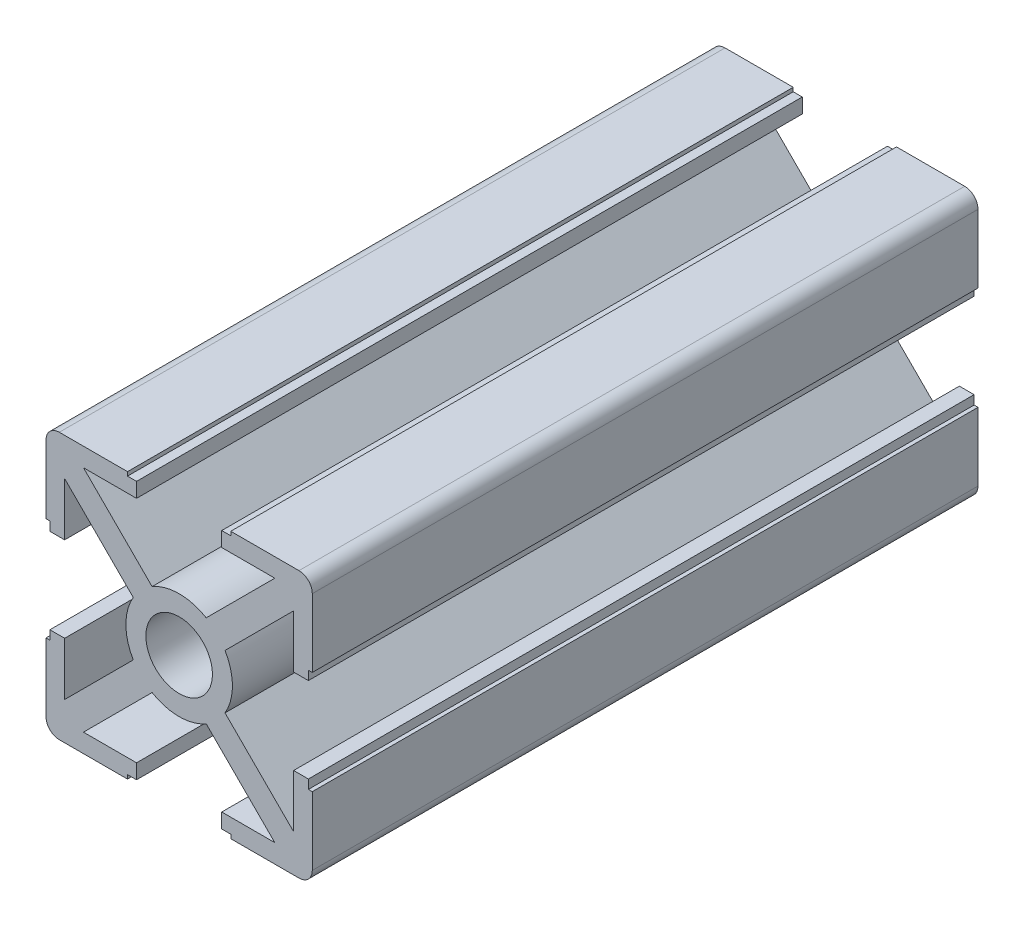
SolidWorks part; units mm, degrees
material "1060 Alloy"
ref_plane "Ön Düzlem" through (0, 0, 0) normal (0, 0, 1) x (1, 0, 0)
ref_plane "Üst Düzlem" through (0, 0, 0) normal (0, 1, 0) x (1, 0, 0)
ref_plane "Sağ Düzlem" through (0, 0, 0) normal (1, 0, 0) x (0, 0, -1)
sketch "Sketch1" plane through (0, 0, 0) normal (0, 0, 1) x (1, 0, 0)
  line L0 (-9.7071, -3.2) -> (-8.6, -3.2)
  line L2 (-10, -3.8775) -> (-10, -9)
  line L3 (-9, -10) -> (-3.8775, -10)
  line L5 (-10, -3.8775) -> (-9.7071, -3.8775)
  line L6 (-10, -10) -> (-9.7071, -9.7071) construction
  line L9 (-3.2, -8.6) -> (-7.1858, -8.6)
  line L10 (-8.6, -3.2) -> (-8.6, -7.1858)
  line L13 (-7.1858, -8.6) -> (-2.0315, -3.4457)
  line L14 (-8.6, -7.1858) -> (-3.4457, -2.0315)
  line L15 (-10.7071, -9.2929) -> (9.2929, 10.7071) construction
  line L16 (-9.2929, -10.7071) -> (10.7071, 9.2929) construction
  line L18 (-10, -10) -> (10, 10) construction
  line L19 (-2.5, 0) -> (-9.7071, 0) construction
  line L20 (0, -2.5) -> (0, -6.9362) construction
  line L21 (-3.2, -8.6) -> (-3.2, -9.7071)
  line L23 (-9.7071, -3.8775) -> (-9.7071, -3.2)
  line L24 (-3.2, -9.7071) -> (-3.8775, -9.7071)
  line L25 (-3.8775, -9.7071) -> (-3.8775, -10)
  line L28 (10, -10) -> (9.7071, -9.7071) construction
  line L30 (3.8775, -9.7071) -> (3.8775, -10)
  line L31 (3.2, -9.7071) -> (3.8775, -9.7071)
  line L32 (9.7071, -3.8775) -> (9.7071, -3.2)
  line L33 (3.2, -8.6) -> (3.2, -9.7071)
  line L34 (8.6, -7.1858) -> (3.4457, -2.0315)
  line L35 (7.1858, -8.6) -> (2.0315, -3.4457)
  line L36 (8.6, -3.2) -> (8.6, -7.1858)
  line L37 (3.2, -8.6) -> (7.1858, -8.6)
  line L38 (10, -3.8775) -> (9.7071, -3.8775)
  line L39 (9, -10) -> (3.8775, -10)
  line L40 (10, -3.8775) -> (10, -9)
  line L41 (9.7071, -3.2) -> (8.6, -3.2)
  line L42 (10, 10) -> (9.7071, 9.7071) construction
  line L43 (0, 2.5) -> (0, 6.9362) construction
  line L44 (-10, 10) -> (-9.7071, 9.7071) construction
  line L45 (9.7071, 3.2) -> (8.6, 3.2)
  line L46 (10, 3.8775) -> (10, 9)
  line L47 (9, 10) -> (3.8775, 10)
  line L48 (10, 3.8775) -> (9.7071, 3.8775)
  line L49 (3.2, 8.6) -> (7.1858, 8.6)
  line L50 (8.6, 3.2) -> (8.6, 7.1858)
  line L51 (7.1858, 8.6) -> (2.0315, 3.4457)
  line L52 (8.6, 7.1858) -> (3.4457, 2.0315)
  line L53 (3.2, 8.6) -> (3.2, 9.7071)
  line L54 (9.7071, 3.8775) -> (9.7071, 3.2)
  line L55 (3.2, 9.7071) -> (3.8775, 9.7071)
  line L56 (3.8775, 9.7071) -> (3.8775, 10)
  line L57 (-3.8775, 9.7071) -> (-3.8775, 10)
  line L58 (-3.2, 9.7071) -> (-3.8775, 9.7071)
  line L59 (-9.7071, 3.8775) -> (-9.7071, 3.2)
  line L60 (-3.2, 8.6) -> (-3.2, 9.7071)
  line L61 (-8.6, 7.1858) -> (-3.4457, 2.0315)
  line L62 (-7.1858, 8.6) -> (-2.0315, 3.4457)
  line L63 (-8.6, 3.2) -> (-8.6, 7.1858)
  line L64 (-3.2, 8.6) -> (-7.1858, 8.6)
  line L65 (-10, 3.8775) -> (-9.7071, 3.8775)
  line L66 (-9, 10) -> (-3.8775, 10)
  line L67 (-10, 3.8775) -> (-10, 9)
  line L68 (-9.7071, 3.2) -> (-8.6, 3.2)
  arc A2 (-10, -9) -> (-9, -10) centre (-9, -9) ccw
  arc A3 (-2.0315, -3.4457) -> (2.0315, -3.4457) centre (0, 0) ccw
  arc A4 (-3.4457, 2.0315) -> (-3.4457, -2.0315) centre (0, 0) ccw
  circle A5 centre (0, 0) radius 2.5
  arc A6 (3.4457, 2.0315) -> (3.4457, -2.0315) centre (0, 0) cw
  arc A7 (10, -9) -> (9, -10) centre (9, -9) cw
  arc A8 (10, 9) -> (9, 10) centre (9, 9) ccw
  arc A9 (-2.0315, 3.4457) -> (2.0315, 3.4457) centre (0, 0) cw
  arc A10 (-10, 9) -> (-9, 10) centre (-9, 9) cw
  dimension "D10" = 1
  dimension "D5" = 1.4
  dimension "D6" = 1.4
  dimension "D7" = 3.2
  dimension "D11" = 3.2
  dimension "D8" = 1
  dimension "D9" = 1
extrude "Boss-Extrude1" add sketch "Sketch1" along normal blind 50
sketch "Sketch2" plane through (0, 10, 0) normal (0, 1, 0) x (1, 0, 0)
  line L0 (-10, -52) -> (10, -52) construction
  circle A0 centre (0, -42) radius 2
  point P4 (0, 0)
  dimension "D1" = 4
  dimension "D2" = 10
extrude "Cut-Extrude1" cut sketch "Sketch2" against normal through all both and the other way through all
